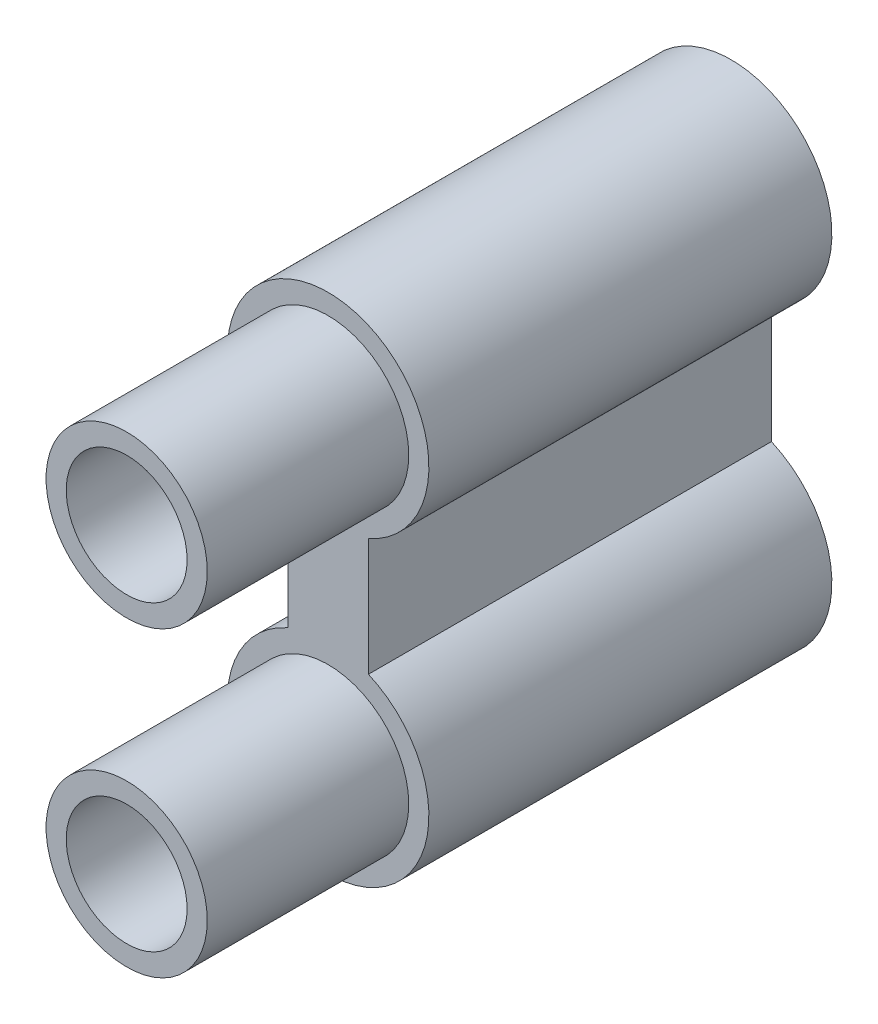
SolidWorks part; units mm, degrees
ref_plane "Plan de face" through (0, 0, 0) normal (0, 0, 1) x (1, 0, 0)
ref_plane "Plan de dessus" through (0, 0, 0) normal (0, 1, 0) x (1, 0, 0)
ref_plane "Plan de droite" through (0, 0, 0) normal (1, 0, 0) x (0, 0, -1)
sketch "Esquisse1" plane through (0, 0, 0) normal (0, 0, 1) x (1, 0, 0)
  line L0 (-10, 52.0871) -> (-10, 22.9129)
  line L2 (10, 22.9129) -> (10, 52.0871)
  circle A0 centre (0, 0) radius 15
  arc A1 (-10, 22.9129) -> (10, 22.9129) centre (0, 0) ccw
  arc A2 (10, 52.0871) -> (-10, 52.0871) centre (0, 75) ccw
  circle A3 centre (0, 75) radius 15
  dimension "D1" = 50
  dimension "D2" = 10
  dimension "D3" = 75
  dimension "D4" = 20
extrude "Boss.-Extru.1" add sketch "Esquisse1" along normal blind 150
sketch "Esquisse3" plane through (0, 0, 150) normal (0, 0, 1) x (1, 0, 0)
  circle A0 centre (0, 75) radius 20
  circle A1 centre (0, 0) radius 20
  dimension "D1" = 40
extrude "Enlèv. mat.-Extru.2" cut sketch "Esquisse3" against normal blind 50 flip side to cut
